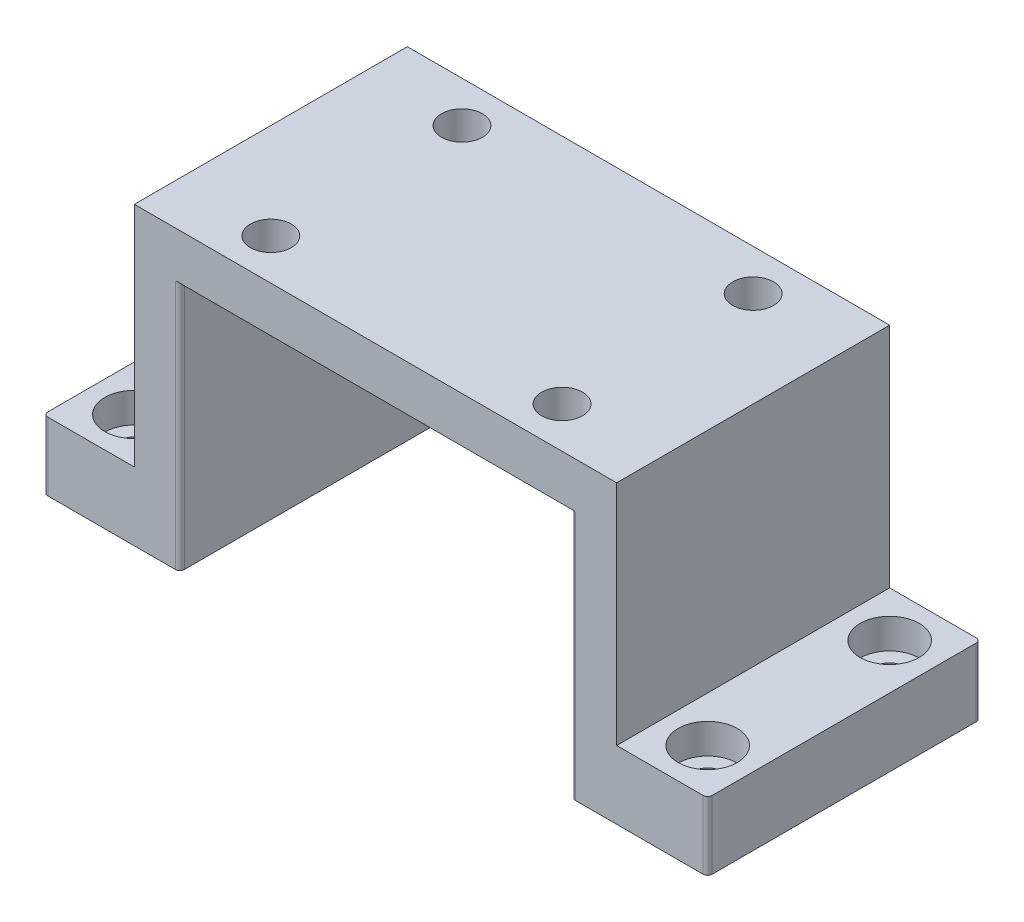
SolidWorks part; units mm, degrees
material "3003 Alloy"
ref_plane "Front Plane" through (0, 0, 0) normal (0, 0, 1) x (1, 0, 0)
ref_plane "Top Plane" through (0, 0, 0) normal (0, 1, 0) x (1, 0, 0)
ref_plane "Right Plane" through (0, 0, 0) normal (1, 0, 0) x (0, 0, -1)
sketch "Sketch1" plane through (0, 0, 0) normal (0, 1, 0) x (1, 0, 0)
  line L1 (-53, -30) -> (53, -30)
  line L2 (-53, -30) -> (-53, 30)
  line L3 (-53, 30) -> (53, 30)
  line L4 (53, -30) -> (53, 30)
  line L5 (-53, -30) -> (53, 30) construction
  line L6 (-53, 30) -> (53, -30) construction
  point P0 (0, 0)
  dimension "D1" = 60
  dimension "D2" = 106
extrude "Boss-Extrude1" add sketch "Sketch1" along normal blind 10
sketch "Sketch2" plane through (0, 0, 0) normal (0, -1, 0) x (1, 0, 0)
  line L0 (53, -30) -> (-53, -30) construction
  line L1 (-53, 30) -> (-43, 30)
  line L2 (-53, 30) -> (-53, -30)
  line L3 (-53, -30) -> (-43, -30)
  line L4 (-43, 30) -> (-43, -30)
  line L6 (53, 30) -> (43, 30)
  line L7 (53, 30) -> (53, -30)
  line L8 (53, -30) -> (43, -30)
  line L9 (43, 30) -> (43, -30)
  dimension "D1" = 10
  dimension "D2" = 10
extrude "Boss-Extrude2" add sketch "Sketch2" along normal blind 55
sketch "Sketch3" plane through (53, 0, 0) normal (1, 0, 0) x (0, 0, -1)
  line L0 (30, 10) -> (30, -55) construction
  line L1 (-30, -55) -> (30, -55)
  line L2 (-30, -55) -> (-30, -40)
  line L3 (-30, -40) -> (30, -40)
  line L4 (30, -55) -> (30, -40)
  dimension "D1" = 15
extrude "Boss-Extrude3" add sketch "Sketch3" along normal blind 20
sketch "Sketch4" plane through (-53, 0, 0) normal (-1, 0, 0) x (0, 0, 1)
  line L0 (30, 10) -> (30, -55) construction
  line L1 (-30, -55) -> (30, -55)
  line L2 (-30, -55) -> (-30, -40)
  line L3 (-30, -40) -> (30, -40)
  line L4 (30, -55) -> (30, -40)
  dimension "D1" = 15
extrude "Boss-Extrude4" add sketch "Sketch4" along normal blind 20
sketch "Sketch5" plane through (0, 10, 0) normal (0, 1, 0) x (1, 0, 0)
  line L0 (0, 0) -> (0, 30) construction
  line L1 (53, 30) -> (-53, 30) construction
  line L2 (0, 0) -> (18.8591, 0) construction
  circle A0 centre (-32, 21) radius 4.5
  circle A1 centre (32, 21) radius 4.5
  circle A2 centre (32, -21) radius 4.5
  circle A3 centre (-32, -21) radius 4.5
  dimension "D3" = 9
  dimension "D1" = 32
  dimension "D2" = 21
extrude "Cut-Extrude1" cut sketch "Sketch5" against normal through all
sketch "Sketch6" plane through (0, -40, 0) normal (0, 1, 0) x (1, 0, 0)
  line L0 (73, 30) -> (53, 30) construction
  line L1 (73, 30) -> (73, -30) construction
  line L2 (73, -30) -> (53, -30) construction
  line L3 (-73, -30) -> (-73, 30) construction
  line L4 (-73, 30) -> (-53, 30) construction
  line L5 (-73, -30) -> (-53, -30) construction
  circle A0 centre (63, 20) radius 6.5
  circle A1 centre (63, -20) radius 6.5
  circle A2 centre (-63, 20) radius 6.5
  circle A3 centre (-63, -20) radius 6.5
  dimension "D2" = 10
  dimension "D9" = 13
  dimension "D10" = 13
  dimension "D11" = 13
  dimension "D12" = 13
  dimension "D1" = 10
  dimension "D3" = 10
  dimension "D4" = 10
  dimension "D5" = 10
  dimension "D6" = 10
  dimension "D7" = 10
  dimension "D8" = 10
extrude "Cut-Extrude2" cut sketch "Sketch6" against normal blind 6.6
sketch "Sketch7" plane through (0, -46.6, 0) normal (0, 1, 0) x (1, 0, 0)
  circle A0 centre (-63, 20) radius 3.3
  circle A1 centre (-63, -20) radius 3.3
  circle A2 centre (63, -20) radius 3.3
  circle A3 centre (63, 20) radius 3.3
  dimension "D1" = 6.6
  dimension "D2" = 6.6
  dimension "D3" = 6.6
  dimension "D4" = 6.6
extrude "Cut-Extrude3" cut sketch "Sketch7" against normal through all
fillet "Fillet1" radius 1 8 edges at (73, -47.5, -30) (43, -27.5, -30) (-43, -27.5, -30) (73, -47.5, 30) (43, -27.5, 30) (-73, -47.5, -30) (-43, -27.5, 30) (-73, -47.5, 30)
